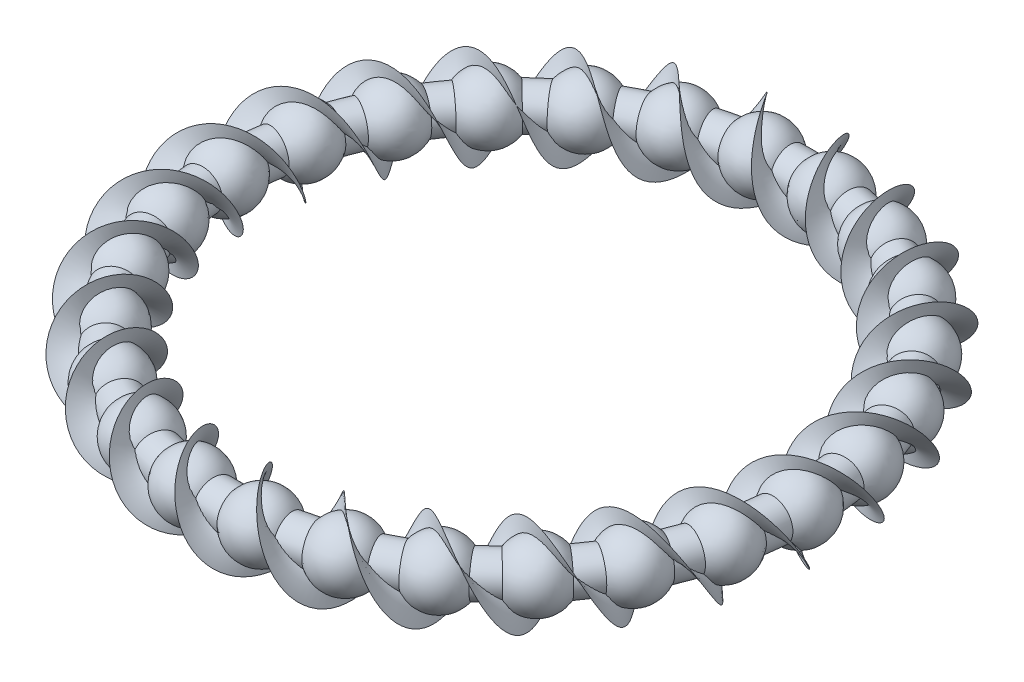
SolidWorks part; units mm, degrees
ref_plane "Front Plane" through (0, 0, 0) normal (0, 0, 1) x (1, 0, 0)
ref_plane "Top Plane" through (0, 0, 0) normal (0, 1, 0) x (1, 0, 0)
ref_plane "Right Plane" through (0, 0, 0) normal (1, 0, 0) x (0, 0, -1)
ref_axis "Axis1" through (0, 55, 0) along (0, -1, 0)
sketch "Sketch1" plane through (0, 0, 0) normal (0, 0, 1) x (1, 0, 0)
  circle A0 centre (50, 0) radius 3.5
  point P2 (0, 0)
  dimension "D1" = 7
  dimension "D2" = 50
revolve "Revolve1" add sketch "Sketch1" angle 360 about axis through (0, 55, 0) along (0, -1, 0)
sketch "Sketch2" plane through (0, 0, 0) normal (0, 0, 1) x (1, 0, 0)
  line L0 (50, 5.5) -> (50, -5.5)
  line L1 (0, 55) -> (0, -55) construction
  arc A0 (50, 5.5) -> (50, -5.5) centre (50, 0) cw
  arc A1 (50, -3.5) -> (50, 3.5) centre (50, 0) ccw construction
  dimension "D1" = 5.5
  dimension "D2" = 50
revolve "Revolve2" add sketch "Sketch2" angle 360 about L0
pattern_circular "CirPattern2" count 26 over 360 about axis through (0, 0, 0) along (0, 1, 0) of "Revolve2"
sketch "Sketch3" plane through (0, 0, 0) normal (0, 0, 1) x (1, 0, 0)
  line L0 (50, 7.5) -> (50, -7.5)
  line L1 (0, 55) -> (0, -55) construction
  dimension "D1" = 15
  dimension "D2" = 50
  dimension "D3" = 7.5
sketch "Sketch4" plane through (0, 0, 0) normal (0, 1, 0) x (1, 0, 0)
  circle A0 centre (0, 0) radius 50
  dimension "D1" = 100
surface "Surface-Sweep1" parameters "D0"=4680
